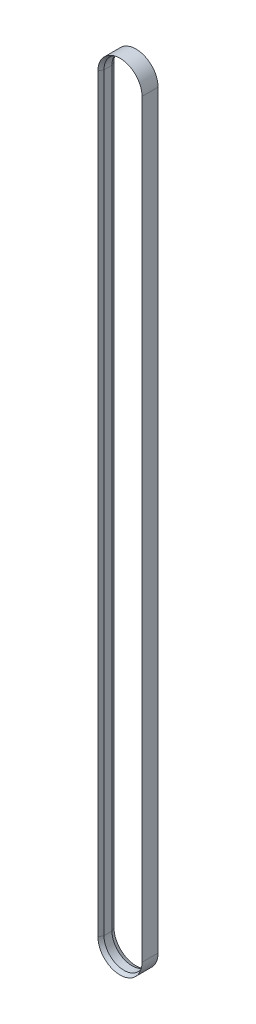
SolidWorks part; units mm, degrees
material "Silicon Rubber"
ref_plane "Front Plane" through (0, 0, 0) normal (0, 0, 1) x (1, 0, 0)
ref_plane "Top Plane" through (0, 0, 0) normal (0, 1, 0) x (1, 0, 0)
ref_plane "Right Plane" through (0, 0, 0) normal (1, 0, 0) x (0, 0, -1)
sketch "Sketch2" plane through (0, 0, 0) normal (0, 0, 1) x (1, 0, 0)
  line L0 (0, 0) -> (1, 0) construction
  line L1 (0, 0) -> (0, 1) construction
  line L2 (25, 0) -> (25, -935.5)
  line L3 (-25, -935.5) -> (-25, 0)
  arc A0 (-25, 0) -> (25, 0) centre (0, 0) cw
  arc A1 (25, -935.5) -> (-25, -935.5) centre (0, -935.5) cw
ref_plane "Plane1" through (0, 0, 0) normal (0, 1, 0) x (1, 0, 0)
sketch "Sketch3" plane through (0, 0, 0) normal (0, 1, 0) x (1, 0, 0)
  line L0 (25, 5) -> (25, -5)
  line L1 (25, -5) -> (27.5, -10)
  line L2 (27.5, -10) -> (27.5, 10)
  line L3 (27.5, 10) -> (25, 5)
  line L4 (-25, 0) -> (25, 0) construction
  dimension "D1" = 5
  dimension "D2" = 10
  dimension "D3" = 20
  dimension "D4" = 10
  dimension "D5" = 25
  dimension "D6" = 2.5
sweep "Sweep1" add profiles "Sketch3" path "Sketch2"
